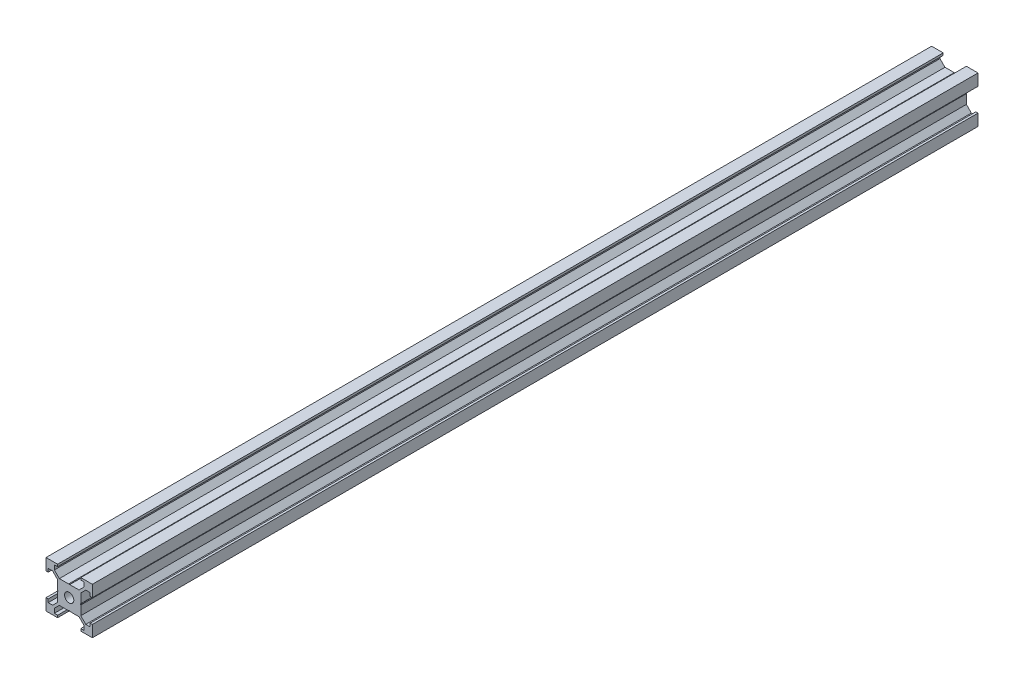
SolidWorks part; units mm, degrees
material "5052-H38"
ref_plane "Front Plane" through (0, 0, 0) normal (0, 0, 1) x (1, 0, 0)
ref_plane "Top Plane" through (0, 0, 0) normal (0, 1, 0) x (1, 0, 0)
ref_plane "Right Plane" through (0, 0, 0) normal (1, 0, 0) x (0, 0, -1)
sketch "Sketch1" plane through (0, 0, 0) normal (0, 0, 1) x (1, 0, 0)
  line L0 (-10, 5) -> (-9.0563, 5)
  line L1 (10, -10) -> (5, -10)
  line L2 (10, -10) -> (10, -5)
  line L3 (10, 10) -> (5, 10)
  line L4 (-10, -10) -> (-10, -5)
  line L5 (10, -10) -> (-10, 10) construction
  line L6 (10, 10) -> (-10, -10) construction
  line L7 (5, -5) -> (0.2457, -5)
  line L8 (5, -5) -> (5, -0.2457)
  line L9 (5, 5) -> (0.2457, 5)
  line L10 (-5, -5) -> (-5, -0.2457)
  line L11 (5, -5) -> (-5, 5) construction
  line L12 (5, 5) -> (-5, -5) construction
  line L13 (-9.0563, 5) -> (-9.0563, 6.4)
  line L14 (-9.0563, 6.4) -> (-7.1563, 6.4)
  line L15 (-7.1563, 6.4) -> (-5, 4.2437)
  line L16 (-5, 10) -> (-5, 9.0563)
  line L17 (-5, 9.0563) -> (-6.4, 9.0563)
  line L18 (-6.4, 9.0563) -> (-6.4, 7.1563)
  line L19 (-6.4, 7.1563) -> (-4.2437, 5)
  line L20 (5, 10) -> (5, 9.0563)
  line L21 (5, 9.0563) -> (6.4, 9.0563)
  line L22 (6.4, 9.0563) -> (6.4, 7.1563)
  line L23 (6.4, 7.1563) -> (4.2437, 5)
  line L24 (7.1563, 6.4) -> (5, 4.2437)
  line L25 (9.0563, 6.4) -> (7.1563, 6.4)
  line L26 (10, 5) -> (9.0563, 5)
  line L27 (9.0563, 5) -> (9.0563, 6.4)
  line L28 (10, -5) -> (9.0563, -5)
  line L29 (9.0563, -5) -> (9.0563, -6.4)
  line L30 (9.0563, -6.4) -> (7.1563, -6.4)
  line L31 (7.1563, -6.4) -> (5, -4.2437)
  line L32 (6.4, -7.1563) -> (4.2437, -5)
  line L33 (6.4, -9.0563) -> (6.4, -7.1563)
  line L34 (5, -10) -> (5, -9.0563)
  line L35 (5, -9.0563) -> (6.4, -9.0563)
  line L36 (-5, -10) -> (-5, -9.0563)
  line L37 (-5, -9.0563) -> (-6.4, -9.0563)
  line L38 (-6.4, -9.0563) -> (-6.4, -7.1563)
  line L39 (-6.4, -7.1563) -> (-4.2437, -5)
  line L40 (-7.1563, -6.4) -> (-5, -4.2437)
  line L41 (-9.0563, -6.4) -> (-7.1563, -6.4)
  line L42 (-10, -5) -> (-9.0563, -5)
  line L43 (-9.0563, -5) -> (-9.0563, -6.4)
  line L44 (0, 0) -> (-5, 0) construction
  line L45 (-5, 0.2457) -> (-4.8279, 0)
  line L46 (-4.8279, 0) -> (-5, -0.2457)
  line L47 (0.2457, 5) -> (0, 4.8279)
  line L48 (0, 4.8279) -> (-0.2457, 5)
  line L49 (5, -0.2457) -> (4.8279, 0)
  line L50 (4.8279, 0) -> (5, 0.2457)
  line L51 (-0.2457, -5) -> (0, -4.8279)
  line L52 (0, -4.8279) -> (0.2457, -5)
  line L53 (-0.2457, 5) -> (-5, 5)
  line L54 (5, 0.2457) -> (5, 5)
  line L55 (-0.2457, -5) -> (-5, -5)
  line L56 (-5, 0.2457) -> (-5, 5)
  line L57 (-10, 5) -> (-10, 10)
  line L58 (-5, 10) -> (-10, 10)
  line L59 (-5, -10) -> (-10, -10)
  line L60 (10, 5) -> (10, 10)
  circle A0 centre (0, 0) radius 2
  point P0 (0, 0)
  point P6 (0, 0)
  point P56 (0, 0)
  point P70 (0, 0)
  dimension "D10" = 4
  dimension "D1" = 20
  dimension "D2" = 10
  dimension "D3" = 1.4
  dimension "D4" = 1.9
  dimension "D5" = 3.0494
  dimension "D7" = 0.3
  dimension "D8" = 35
  dimension "D6" = 4
  dimension "D9" = 4
extrude "Boss-Extrude1" add sketch "Sketch1" along normal blind 382 contours L26 L60 L3 L20 L21 L22 L23 L9 L54 L24 L25 L27 | L56 L45 L46 L10 L55 L51 L52 L7 L8 L49 L50 L54 L9 L47 L48 L53 A0 | L16 L58 L57 L0 L13 L14 L15 L56 L53 L19 L18 L17 | L59 L36 L37 L38 L39 L55 L10 L40 L41 L43 L42 L4 | L35 L34 L1 L2 L28 L29 L30 L31 L8 L7 L32 L33
